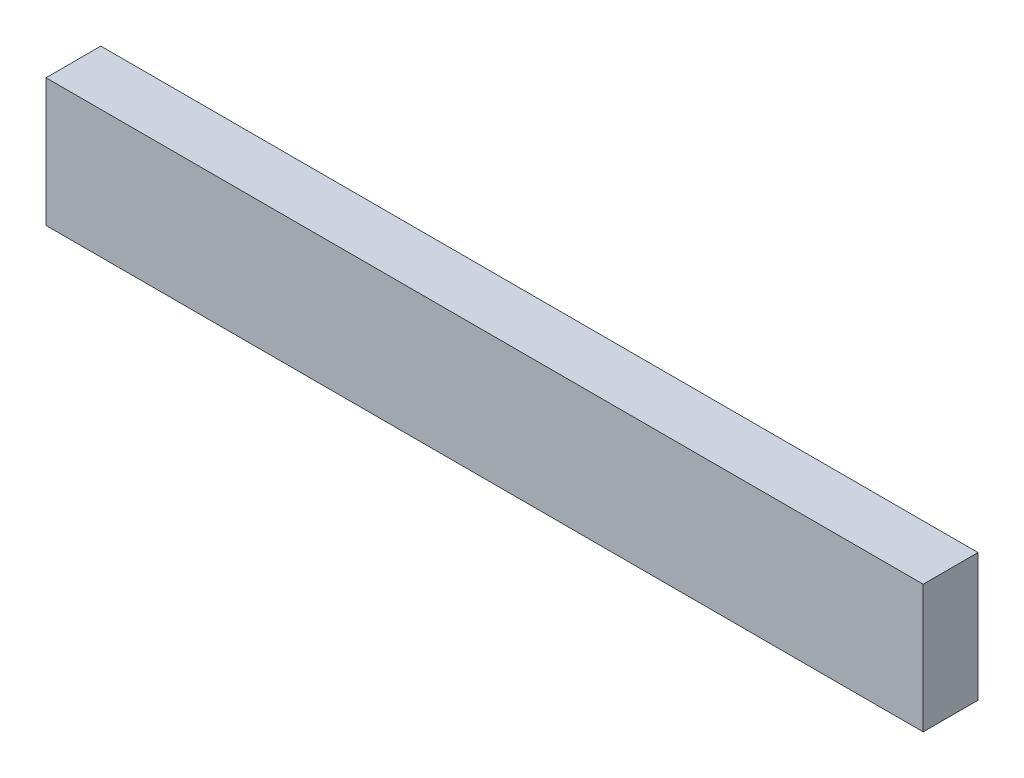
SolidWorks part; units mm, degrees
material "Oak"
ref_plane "Front Plane" through (0, 0, 0) normal (0, 0, 1) x (1, 0, 0)
ref_plane "Top Plane" through (0, 0, 0) normal (0, 1, 0) x (1, 0, 0)
ref_plane "Right Plane" through (0, 0, 0) normal (1, 0, 0) x (0, 0, -1)
sketch "Sketch1" plane through (0, 0, 0) normal (1, 0, 0) x (0, 0, -1)
  line L1 (-19.05, -44.45) -> (19.05, -44.45)
  line L2 (-19.05, -44.45) -> (-19.05, 44.45)
  line L3 (-19.05, 44.45) -> (19.05, 44.45)
  line L4 (19.05, -44.45) -> (19.05, 44.45)
  line L5 (-19.05, -44.45) -> (19.05, 44.45) construction
  line L6 (-19.05, 44.45) -> (19.05, -44.45) construction
  point P0 (0, 0)
  dimension "D1" = 38.1
  dimension "D2" = 88.9
extrude "Boss-Extrude1" add sketch "Sketch1" along normal blind 609.6
